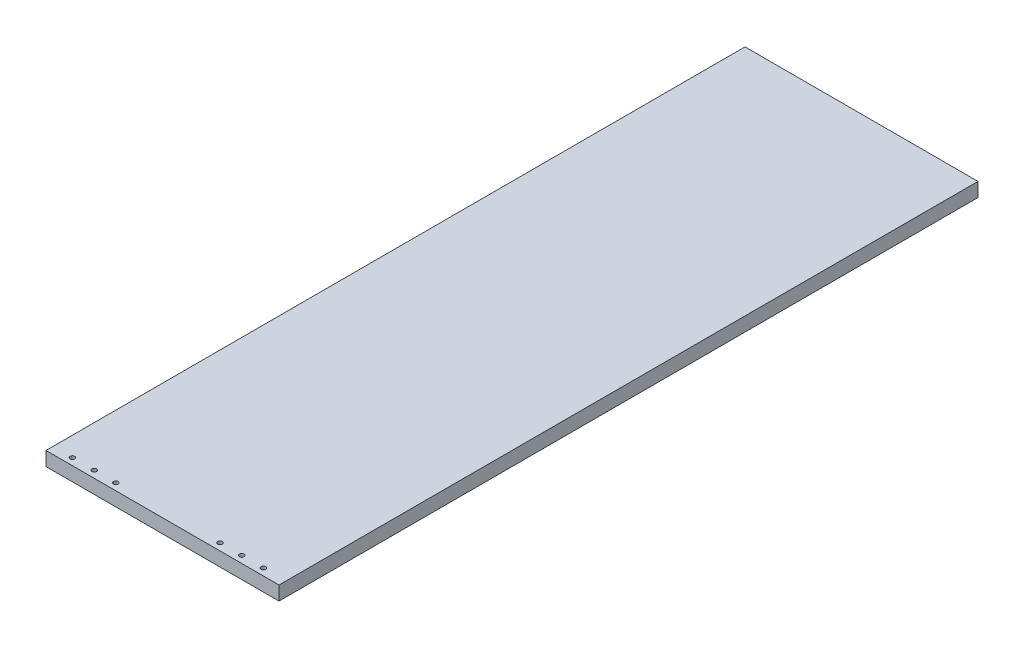
SolidWorks part; units mm, degrees
ref_plane "Спереди" through (0, 0, 0) normal (0, 0, 1) x (1, 0, 0)
ref_plane "Сверху" through (0, 0, 0) normal (0, 1, 0) x (1, 0, 0)
ref_plane "Справа" through (0, 0, 0) normal (1, 0, 0) x (0, 0, -1)
sketch "Эскиз2" plane through (0, 0, 0) normal (0, 1, 0) x (1, 0, 0)
  line L1 (0, 0) -> (300, 0)
  line L2 (0, 0) -> (0, 900)
  line L3 (0, 900) -> (300, 900)
  line L4 (300, 0) -> (300, 900)
extrude "Бобышка-Вытянуть1" add sketch "Эскиз2" along normal blind 18
sketch "Эскиз3" plane through (0, 18, 0) normal (0, 1, 0) x (1, 0, 0)
  circle A0 centre (25, 9) radius 3
  circle A1 centre (53, 9) radius 3
  circle A2 centre (81, 9) radius 3
  circle A3 centre (215, 9) radius 3
  circle A4 centre (243, 9) radius 3
  circle A5 centre (271, 9) radius 3
  dimension "D1" = 3
  dimension "D2" = 2
extrude "Вырез-Вытянуть1" cut sketch "Эскиз3" against normal blind 9
